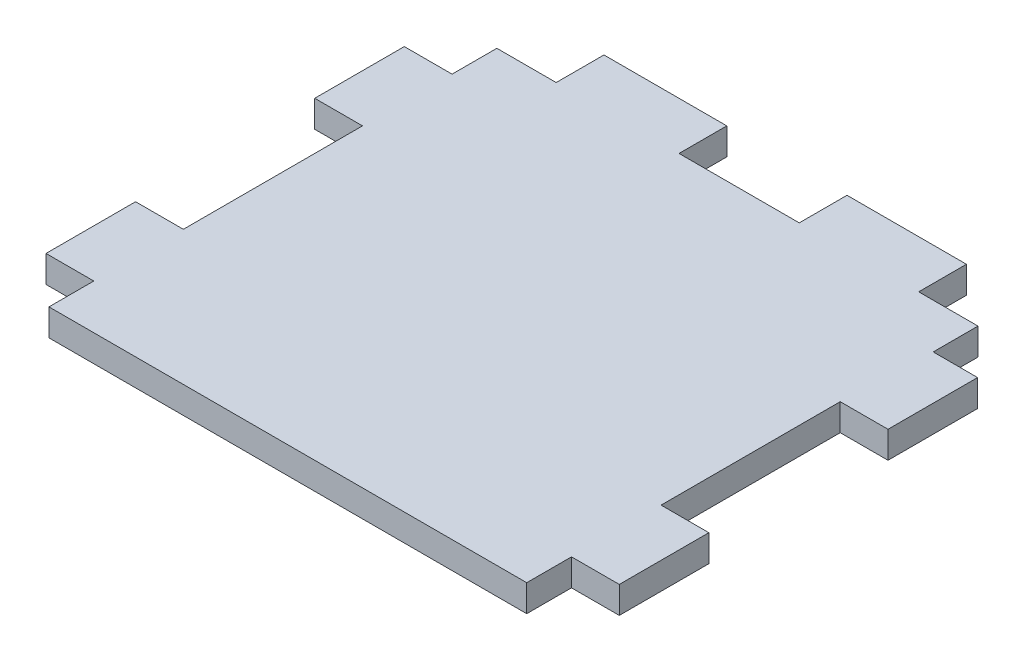
SolidWorks part; units mm, degrees
ref_plane "Front Plane" through (0, 0, 0) normal (0, 0, 1) x (1, 0, 0)
ref_plane "Top Plane" through (0, 0, 0) normal (0, 1, 0) x (1, 0, 0)
ref_plane "Right Plane" through (0, 0, 0) normal (1, 0, 0) x (0, 0, -1)
sketch "Sketch1" plane through (0, 0, 0) normal (0, 1, 0) x (1, 0, 0)
  line L0 (-40, 37.5) -> (-30.0663, 37.5)
  line L1 (-40, 37.5) -> (-30.0663, 37.5)
  line L3 (-45, -37.5) -> (45, -37.5)
  line L5 (-45, 37.5) -> (-40, 33.3333) construction
  line L6 (-45, -37.5) -> (-40, -33.3333) construction
  line L12 (-40, 37.5) -> (-40, 30)
  line L13 (-30.0663, 45.5) -> (-9.4963, 45.5)
  line L14 (-30.0663, 45.5) -> (-30.0663, 37.5)
  line L16 (-9.4963, 45.5) -> (-9.4963, 37.5)
  line L18 (-9.4963, 37.5) -> (10.6363, 37.5)
  line L19 (45, -37.5) -> (40, -33.3333) construction
  line L21 (45, 32.5) -> (40, 28.3333) construction
  line L37 (40, -32.5) -> (40, -37.5)
  line L38 (-48, 15) -> (-48, 30)
  line L49 (-40, 12.5) -> (-40, -15)
  line L50 (-40, -32.5) -> (-40, -37.5)
  line L51 (-40, -32.5) -> (-40, -34.2716)
  line L52 (40.57, 30) -> (40.57, 37.5)
  line L56 (48, -30) -> (48, -17.5)
  line L58 (40, 15) -> (48, 15)
  line L61 (10.6363, 45.5) -> (10.6363, 37.5)
  line L62 (30.6363, 45.5) -> (30.6363, 37.5)
  line L63 (30.6363, 45.5) -> (10.6363, 45.5)
  line L64 (40.57, 37.5) -> (30.6363, 37.5)
  line L65 (40.57, 37.5) -> (30.6363, 37.5)
  line L66 (48, 15) -> (48, 30)
  line L67 (48, 30) -> (40.57, 30)
  line L70 (40, 12.5) -> (40, -15)
  line L73 (-40, -15) -> (-48, -15)
  line L74 (-48, -15) -> (-48, -30)
  line L75 (-40, -30) -> (-40, -32.5)
  line L77 (-40, 30) -> (-48, 30)
  line L78 (-40, 12.5) -> (-40, 15)
  line L79 (-40, 15) -> (-48, 15)
  line L80 (-48, -30) -> (-40, -30)
  line L81 (40, 15) -> (40, 12.5)
  line L82 (40, -15) -> (48, -15)
  line L83 (48, -15) -> (48, -30)
  line L84 (48, -30) -> (40, -30)
  line L85 (40, -32.5) -> (40, -30)
  point P0 (0, 0)
  dimension "D1" = 20.1325
  dimension "D2" = 80
  dimension "D3" = 15
  dimension "D4" = 8
  dimension "D5" = 20.57
  dimension "D9" = 2.5
extrude "Boss-Extrude1" add sketch "Sketch1" against normal blind 4.5
